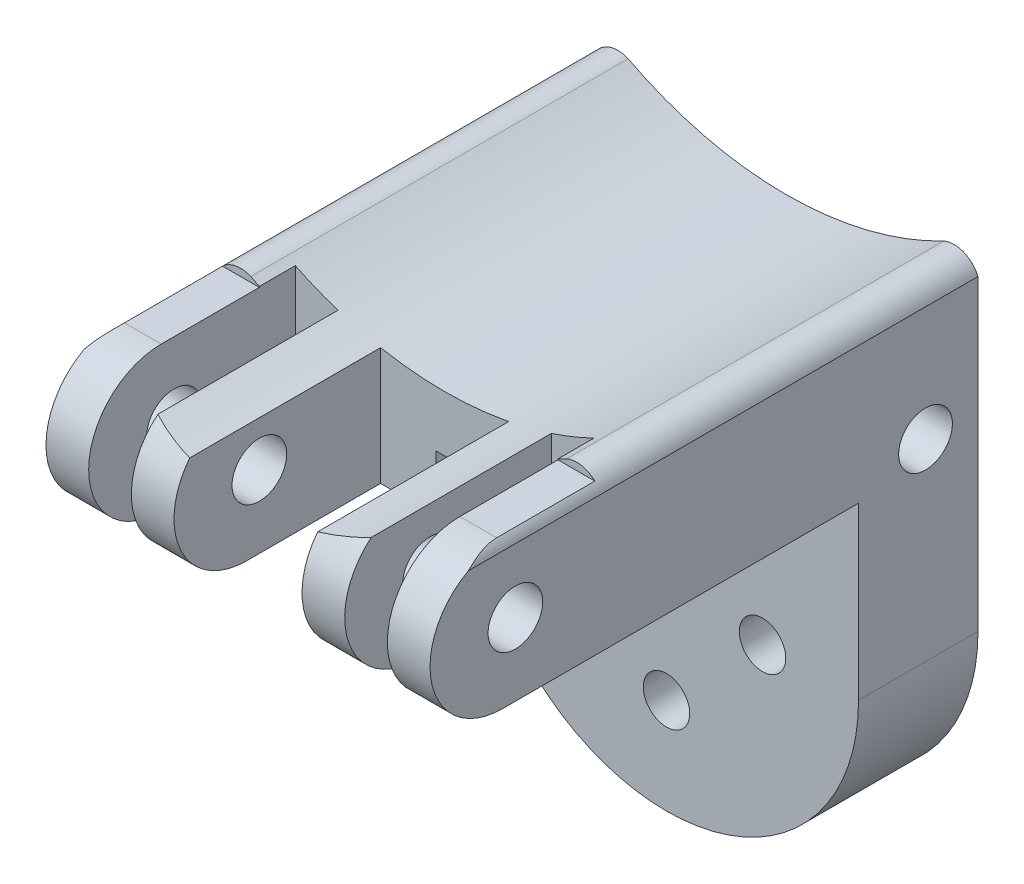
SolidWorks part; units mm, degrees
ref_plane "Front Plane" through (0, 0, 0) normal (0, 0, 1) x (1, 0, 0)
ref_plane "Top Plane" through (0, 0, 0) normal (0, 1, 0) x (1, 0, 0)
ref_plane "Right Plane" through (0, 0, 0) normal (1, 0, 0) x (0, 0, -1)
sketch "Sketch1" plane through (0, 0, 0) normal (0, 1, 0) x (1, 0, 0)
  line L0 (-17.5, 328) -> (-22.5, 328)
  line L2 (-7.5, 328) -> (-12.5, 328)
  line L34 (-2.5, 352.2085) -> (2.5, 352.2085)
  line L68 (-12.5, 328) -> (-12.5, 352.2085)
  line L70 (-17.5, 328) -> (-17.5, 352.2085)
  line L71 (-17.5, 352.2085) -> (-12.5, 352.2085)
  line L72 (-7.5, 328) -> (-7.5, 352.2085)
  line L73 (-7.5, 352.2085) -> (-2.5, 352.2085)
  line L77 (2.5, 352.2085) -> (7.5, 352.2085)
  line L78 (7.5, 352.2085) -> (7.5, 328)
  line L79 (7.5, 328) -> (12.5, 328)
  line L80 (12.5, 328) -> (12.5, 352.2085)
  line L81 (12.5, 352.2085) -> (17.5, 352.2085)
  line L82 (17.5, 352.2085) -> (17.5, 328)
  line L83 (17.5, 328) -> (22.5, 328)
  line L85 (22.5, 328) -> (22.5, 392.2085)
  line L86 (22.5, 392.2085) -> (-22.5, 392.2085)
  line L87 (-22.5, 392.2085) -> (-22.5, 328)
extrude "Boss-Extrude1" add sketch "Sketch1" along normal blind 20
sketch "Sketch2" plane through (0, 0, 50) normal (0, 0, 1) x (1, 0, 0)
  line L0 (-22.5, 20) -> (22.5, 20)
  line L1 (-22.5, 20) -> (-22.5, 16)
  line L2 (-22.5, 20) -> (-22.5, 0) construction
  line L4 (22.5, 20) -> (22.5, 0) construction
  line L5 (22.5, 16) -> (22.5, 20)
  arc A0 (-18.5, 17.6071) -> (18.5, 17.6071) centre (0, 53.0719) ccw
  arc A1 (-22.5, 16) -> (-18.5, 17.6071) centre (-19.6964, 14.8036) cw
  arc A2 (18.5, 17.6071) -> (22.5, 16) centre (19.6964, 14.8036) cw
sketch "Sketch8" plane through (22.5, 0, 0) normal (1, 0, 0) x (0, 0, -1)
  line L10 (328, 20) -> (328, 0)
  line L11 (336.5, 20) -> (328, 20)
  line L12 (328, 0) -> (328, 17)
  line L13 (336.5, 0) -> (328, 0)
  line L18 (336.5, 17) -> (348, 17)
  line L19 (348, 17) -> (348, 20)
  line L20 (348, 20) -> (336.5, 20)
  arc A2 (336.5, 0) -> (336.5, 17) centre (336.5, 8.5) cw
extrude "Cut-Extrude23" cut sketch "Sketch2" against normal blind 444
sketch "Sketch12" plane through (0, 0, 50) normal (0, 0, 1) x (1, 0, 0)
  line L0 (-1, 3.35) -> (-1, 6.55)
  line L3 (1, 3.35) -> (-1, 3.35)
  line L4 (1, 6.55) -> (1, 3.35)
  line L5 (0, 6.55) -> (1, 6.55)
  line L6 (0, 6.55) -> (-1, 6.55)
extrude "Cut-Extrude26" cut sketch "Sketch12" against normal blind 444
sketch "Sketch14" plane through (0, 0, -392.2085) normal (0, 0, -1) x (-1, 0, 0)
  line L0 (-22.5, 0) -> (-22.5, -20)
  line L2 (22.5, -20) -> (22.5, 0)
  line L3 (22.5, 16) -> (22.5, 0) construction
  line L4 (-22.5, 0) -> (22.5, 0) construction
  line L5 (22.5, 0) -> (-22.5, 0)
  arc A0 (-22.5, -20) -> (22.5, -20) centre (0, -20) ccw
extrude "Boss-Extrude2" add sketch "Sketch14" against normal blind 14
sketch "Sketch15" plane through (0, 0, -392.2085) normal (0, 0, -1) x (-1, 0, 0)
  circle A1 centre (11.25, -20) radius 2.72
  circle A2 centre (0, -6.75) radius 2.72
  circle A3 centre (-11.25, -20) radius 2.72
  circle A4 centre (0, -31.25) radius 2.72
extrude "Cut-Extrude27" cut sketch "Sketch15" against normal blind 14
sketch "Sketch16" plane through (-22.5, 0, 0) normal (-1, 0, 0) x (0, 0, 1)
  circle A0 centre (-1.25, 8.5) radius 3.25
  circle A2 centre (-386.0585, 2.5888) radius 3.15
extrude "Cut-Extrude28" cut sketch "Sketch16" against normal blind 45
sketch "Sketch17" plane through (0, 0, -392.2085) normal (0, 0, -1) x (-1, 0, 0)
  line L0 (1, 8.5) -> (5, 8.5)
  line L1 (5, 8.5) -> (5, 2.5)
  line L2 (-1, 8.5) -> (-5, 8.5)
  line L3 (-5, 8.5) -> (-5, 2.5)
  line L4 (-5, 2.5) -> (5, 2.5)
  line L5 (5, 2.5) -> (4.6917, 2.6274)
  line L6 (-1, 8.5) -> (1, 8.5)
extrude "Cut-Extrude29" cut sketch "Sketch17" against normal blind 6.15
extrude "Cut-Extrude31" cut sketch "Sketch8" against normal blind 45 contours L13 A2 L12 | L10 A2 L18 L19 L20 L11
sketch "Sketch18" plane through (22.5, 0, 0) normal (1, 0, 0) x (0, 0, -1)
  circle A1 centre (338, 8.5) radius 3.2
extrude "Cut-Extrude32" cut sketch "Sketch18" against normal blind 45
